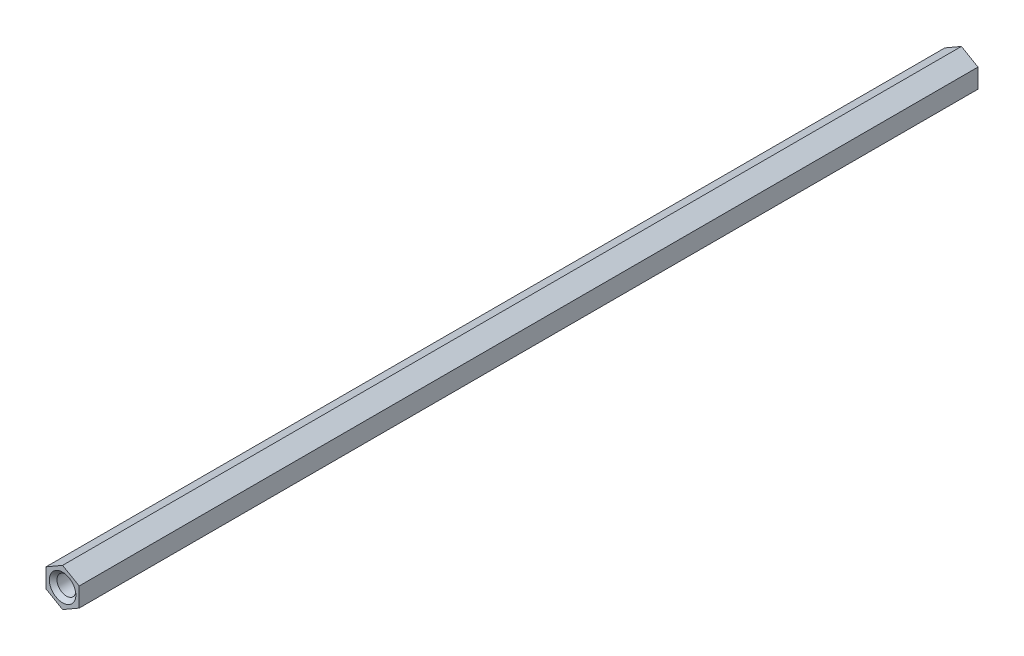
SolidWorks part; units mm, degrees
ref_plane "Front Plane" through (0, 0, 0) normal (0, 0, 1) x (1, 0, 0)
ref_plane "Top Plane" through (0, 0, 0) normal (0, 1, 0) x (1, 0, 0)
ref_plane "Right Plane" through (0, 0, 0) normal (1, 0, 0) x (0, 0, -1)
sketch "Sketch1" plane through (0, 0, 0) normal (0, 0, 1) x (1, 0, 0)
  line L0 (-4.7625, 0) -> (4.7625, 0) construction
  line L9 (0, 5.4993) -> (-4.7625, 2.7496) construction
  line L10 (-4.7625, 2.7496) -> (-4.7625, -2.7496) construction
  line L11 (-4.7625, -2.7496) -> (0, -5.4993) construction
  line L12 (0, -5.4993) -> (4.7625, -2.7496) construction
  line L13 (4.7625, -2.7496) -> (4.7625, 2.7496) construction
  line L14 (4.7625, 2.7496) -> (0, 5.4993) construction
  circle A3 centre (0, 0) radius 4.7625 construction
  point P4 (0, 0)
  dimension "Width" = 9.525
sketch "Sketch2" plane through (0, 0, 0) normal (1, 0, 0) x (0, 0, -1)
  line L0 (129, 5.4993) -> (-129, 5.4993) construction
  point P3 (-118.0463, 5.4993)
  point P4 (0, 5.4993)
  point P5 (118.0463, 5.4993)
  dimension "Length" = 258
  dimension "D1" = 10.9537
  dimension "D2" = 10.9537
sketch "Sketch3" plane through (0, 0, 0) normal (0, 0, 1) x (1, 0, 0)
  line L1 (0, 5.4993) -> (4.7625, 2.7496)
  line L2 (4.7625, 2.7496) -> (4.7625, -2.7496)
  line L3 (4.7625, -2.7496) -> (0, -5.4993)
  line L4 (0, -5.4993) -> (-4.7625, -2.7496)
  line L5 (-4.7625, -2.7496) -> (-4.7625, 2.7496)
  line L6 (-4.7625, 2.7496) -> (0, 5.4993)
extrude "Boss-Extrude1" add sketch "Sketch3" along normal mid plane 258
sketch "Sketch6" plane through (0, 0, 129) normal (0, 0, 1) x (1, 0, 0)
  point P0 (0, 0)
hole_wizard "1/4-28 Tapped Hole1" positions "Sketch6" profile "Sketch5" tap size "1/4-28" standard "ANSI Inch"
sketch "Sketch5" plane through (0, 0, 129) normal (1, 0, 0) x (0, -1, 0)
  line L0 (0, 0) -> (0, 16.8654)
  line L1 (0, 16.8654) -> (2.7051, 15.24)
  line L2 (2.7051, 15.24) -> (2.7051, 1.1049)
  line L3 (2.7051, 1.1049) -> (3.81, 0)
  line L5 (3.81, 0) -> (0, 0)
  line L6 (-2.7051, 1.1049) -> (-3.81, 0) construction
  line L10 (0, 16.8654) -> (-2.7051, 15.24) construction
  line L11 (0, -6.35) -> (0, 107.95) construction
  dimension "Tap Drill Dia." = 5.4102
  dimension "Tap Drill Depth" = 15.24
  dimension "Near C'Sink Dia." = 7.62
  dimension "Near C'Sink Angle" = 90
  dimension "Drill Angle" = 118
cosmetic thread "Hole Thread1"
sketch "Sketch9" plane through (0, 0, -129) normal (0, 0, -1) x (-1, 0, 0)
  point P0 (0, 0)
hole_wizard "1/4-28 Tapped Hole2" positions "Sketch9" profile "Sketch8" tap size "1/4-28" standard "ANSI Inch"
cosmetic thread "Hole Thread2"
sketch "Sketch8" plane through (0, 0, -129) normal (1, 0, 0) x (0, 1, 0)
  line L0 (0, 0) -> (0, 18.8593)
  line L1 (0, 18.8593) -> (2.7051, 17.2339)
  line L2 (2.7051, 17.2339) -> (2.7051, 1.1049)
  line L3 (2.7051, 1.1049) -> (3.81, 0)
  line L5 (3.81, 0) -> (0, 0)
  line L6 (-2.7051, 1.1049) -> (-3.81, 0) construction
  line L10 (0, 18.8593) -> (-2.7051, 17.2339) construction
  line L11 (0, -6.35) -> (0, 107.95) construction
  dimension "Tap Drill Dia." = 5.4102
  dimension "Tap Drill Depth" = 17.2339
  dimension "Near C'Sink Dia." = 7.62
  dimension "Near C'Sink Angle" = 90
  dimension "Drill Angle" = 118
equation "\"D1@Boss-Extrude1\" = \"Length@Sketch2\""
equation "\"D1@Sketch2\" = \"Width@Sketch1\" * 1.15"
equation "\"D2@Sketch2\"=\"D1@Sketch2\""
